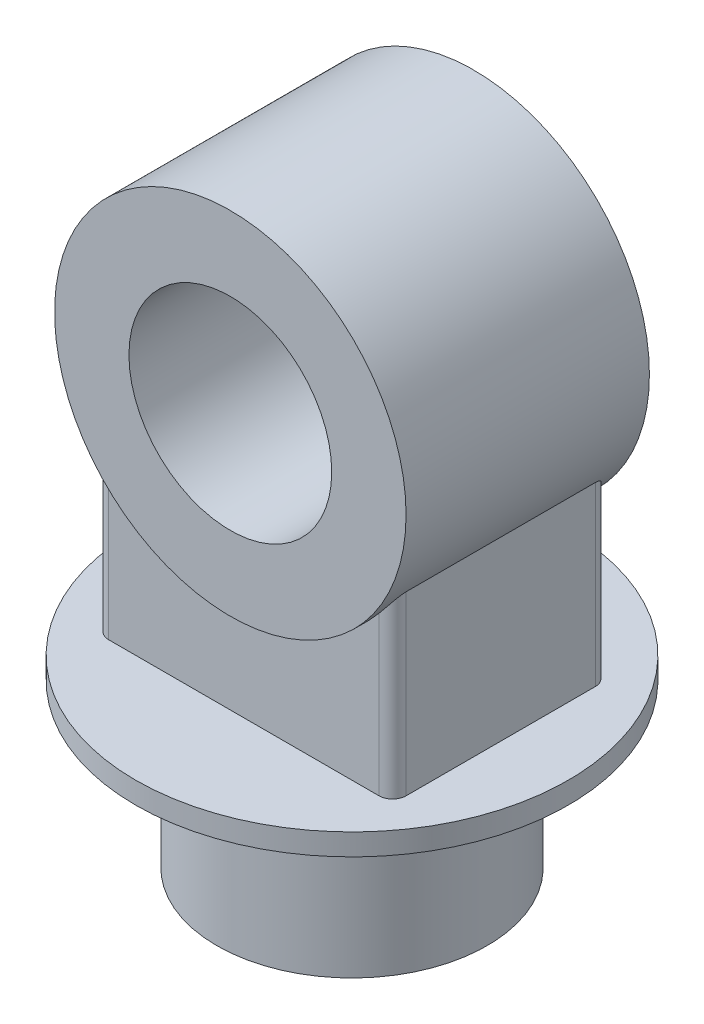
SolidWorks part; units mm, degrees
material "ABS"
ref_plane "Front Plane" through (0, 0, 0) normal (0, 0, 1) x (1, 0, 0)
ref_plane "Top Plane" through (0, 0, 0) normal (0, 1, 0) x (1, 0, 0)
ref_plane "Right Plane" through (0, 0, 0) normal (1, 0, 0) x (0, 0, -1)
sketch "Sketch1" plane through (0, 0, 0) normal (0, 1, 0) x (1, 0, 0)
  circle A0 centre (0, 0) radius 100
  dimension "D1" = 200
extrude "Boss-Extrude1" add sketch "Sketch1" along normal blind 120
sketch "Sketch2" plane through (0, 120, 0) normal (0, 1, 0) x (1, 0, 0)
  circle A0 centre (0, 0) radius 160
  dimension "D1" = 320
extrude "Boss-Extrude2" add sketch "Sketch2" along normal blind 16
sketch "Sketch3" plane through (0, 0, 0) normal (0, 0, 1) x (1, 0, 0)
  line L2 (160, 136) -> (-160, 136) construction
  circle A1 centre (0, 336) radius 130
  circle A2 centre (0, 336) radius 75
  dimension "D1" = 260
  dimension "D2" = 150
  dimension "D3" = 200
extrude "Boss-Extrude3" add sketch "Sketch3" along normal mid plane 180 separate body
sketch "Sketch4" plane through (0, 136, 0) normal (0, 1, 0) x (1, 0, 0)
  line L1 (110, -80) -> (-110, -80)
  line L2 (110, -80) -> (110, 80)
  line L3 (110, 80) -> (-110, 80)
  line L4 (-110, -80) -> (-110, 80)
  line L5 (110, -80) -> (-110, 80) construction
  line L6 (110, 80) -> (-110, -80) construction
  point P0 (0, 0)
  dimension "D1" = 220
  dimension "D2" = 160
extrude "Boss-Extrude4" add sketch "Sketch4" along normal up to next
fillet "Fillet1" radius 10 4 edges at (-110, 201.359, 80) (-110, 201.359, -80) (110, 201.359, -80) (110, 201.359, 80)
